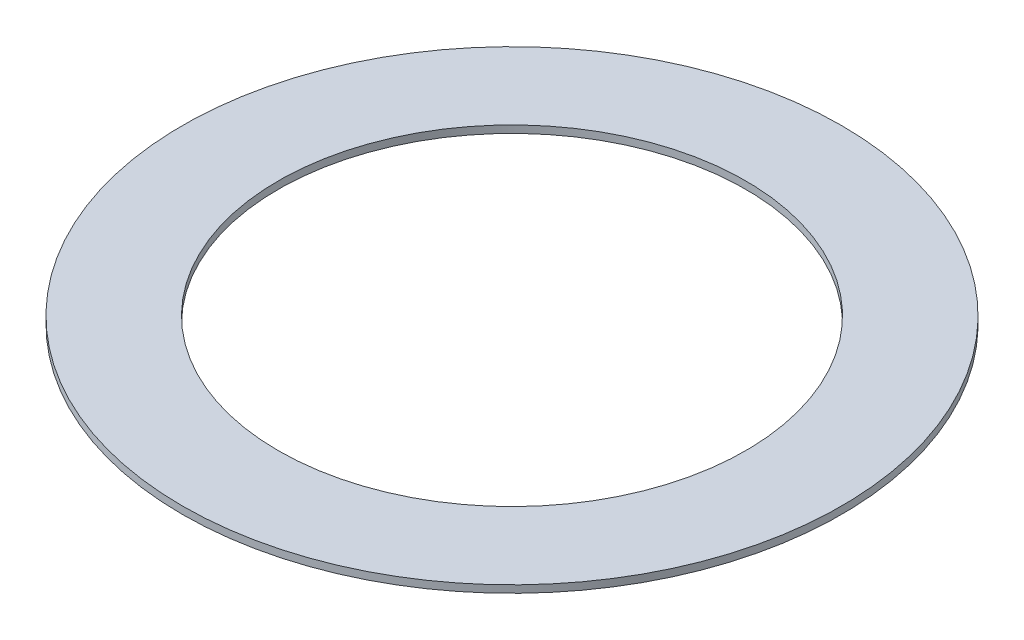
SolidWorks part; units mm, degrees
material "Oak"
ref_plane "Front Plane" through (0, 0, 0) normal (0, 0, 1) x (1, 0, 0)
ref_plane "Top Plane" through (0, 0, 0) normal (0, 1, 0) x (1, 0, 0)
ref_plane "Right Plane" through (0, 0, 0) normal (1, 0, 0) x (0, 0, -1)
sketch "Sketch1" plane through (0, 0, 0) normal (0, 1, 0) x (1, 0, 0)
  circle A0 centre (0, 0) radius 76.2
  circle A1 centre (0, 0) radius 107.442
  dimension "D1" = 152.4
  dimension "D2" = 214.884
extrude "Boss-Extrude1" add sketch "Sketch1" along normal blind 2.4
